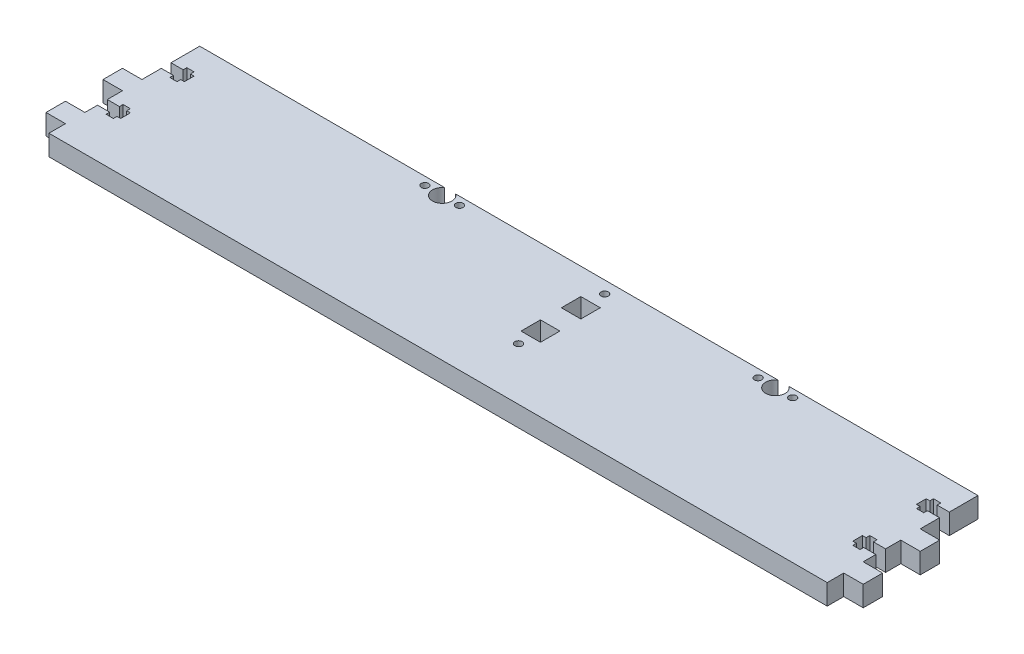
SolidWorks part; units mm, degrees
ref_plane "Front Plane" through (0, 0, 0) normal (0, 0, 1) x (1, 0, 0)
ref_plane "Top Plane" through (0, 0, 0) normal (0, 1, 0) x (1, 0, 0)
ref_plane "Right Plane" through (0, 0, 0) normal (1, 0, 0) x (0, 0, -1)
sketch "Sketch1" plane through (0, 0, 0) normal (0, 1, 0) x (1, 0, 0)
  line L0 (0, 31) -> (0, -31) construction
  line L1 (-160, 31) -> (-59.2605, 31)
  line L2 (-160, 31) -> (-160, 19.2)
  line L3 (-160, -31) -> (160, -31)
  line L4 (160, 31) -> (160, 19.2)
  line L5 (-160, 31) -> (160, -31) construction
  line L6 (-160, -31) -> (160, 31) construction
  line L7 (11.5, 31) -> (11.5, -31) construction
  line L8 (80, 27.7) -> (80, 23.7) construction
  line L9 (72.9, 27.7) -> (87.1, 27.7) construction
  line L10 (82.2605, 31) -> (160, 31)
  line L11 (160, 17.2) -> (150.5, 17.2) construction
  line L12 (160, 19.2) -> (155, 19.2)
  line L13 (155, 19.2) -> (155, 20.7)
  line L14 (155, 20.7) -> (152, 20.7)
  line L15 (152, 20.7) -> (152, 19.2)
  line L16 (152, 19.2) -> (150.5, 19.2)
  line L17 (150.5, 19.2) -> (150.5, 15.2)
  line L18 (152, 15.2) -> (150.5, 15.2)
  line L19 (152, 13.7) -> (152, 15.2)
  line L20 (155, 13.7) -> (152, 13.7)
  line L21 (155, 15.2) -> (155, 13.7)
  line L22 (160, 15.2) -> (155, 15.2)
  line L23 (160, 15.2) -> (160, 7.2486)
  line L24 (160, 4.1) -> (0, 4.1) construction
  line L25 (160, -9) -> (150.5, -9) construction
  line L26 (160, -7) -> (155, -7)
  line L27 (155, -7) -> (155, -5.5)
  line L28 (155, -5.5) -> (152, -5.5)
  line L29 (152, -5.5) -> (152, -7)
  line L30 (152, -7) -> (150.5, -7)
  line L31 (150.5, -11) -> (150.5, -7)
  line L32 (152, -11) -> (150.5, -11)
  line L33 (152, -12.5) -> (152, -11)
  line L34 (155, -12.5) -> (152, -12.5)
  line L35 (155, -11) -> (155, -12.5)
  line L36 (160, -11) -> (155, -11)
  line L37 (160, -11) -> (160, -16.2)
  line L38 (160, 7.2486) -> (168, 7.2486)
  line L39 (168, 7.2486) -> (168, -0.7514)
  line L40 (168, -0.7514) -> (160, -0.7514)
  line L41 (160, -8.4757) -> (0, -8.4757) construction
  line L42 (168, -16.2) -> (160, -16.2)
  line L43 (168, -24.2) -> (168, -16.2)
  line L44 (160, -24.2) -> (168, -24.2)
  line L45 (160, -24.2) -> (160, -31)
  line L46 (160, -0.7514) -> (160, -7)
  line L47 (-49.9, 27.7) -> (-64.1, 27.7) construction
  line L48 (-57, 27.7) -> (-57, 23.7) construction
  line L49 (-160, -9) -> (-150.5, -9) construction
  line L50 (-160, 17.2) -> (-150.5, 17.2) construction
  line L51 (-160, -0.7514) -> (-160, -7)
  line L52 (-160, -24.2) -> (-168, -24.2)
  line L53 (-168, -24.2) -> (-168, -16.2)
  line L54 (-168, -16.2) -> (-160, -16.2)
  line L55 (-168, -0.7514) -> (-160, -0.7514)
  line L56 (-168, 7.2486) -> (-168, -0.7514)
  line L57 (-160, 7.2486) -> (-168, 7.2486)
  line L58 (-160, -11) -> (-160, -16.2)
  line L59 (-160, -11) -> (-155, -11)
  line L60 (-155, -11) -> (-155, -12.5)
  line L61 (-155, -12.5) -> (-152, -12.5)
  line L62 (-152, -12.5) -> (-152, -11)
  line L63 (-152, -11) -> (-150.5, -11)
  line L64 (-150.5, -11) -> (-150.5, -7)
  line L65 (-152, -7) -> (-150.5, -7)
  line L66 (-152, -5.5) -> (-152, -7)
  line L67 (-155, -5.5) -> (-152, -5.5)
  line L68 (-155, -7) -> (-155, -5.5)
  line L69 (-160, -7) -> (-155, -7)
  line L70 (-160, 15.2) -> (-160, 7.2486)
  line L71 (-160, 15.2) -> (-155, 15.2)
  line L72 (-155, 15.2) -> (-155, 13.7)
  line L73 (-155, 13.7) -> (-152, 13.7)
  line L74 (-152, 13.7) -> (-152, 15.2)
  line L75 (-152, 15.2) -> (-150.5, 15.2)
  line L76 (-150.5, 19.2) -> (-150.5, 15.2)
  line L77 (-152, 19.2) -> (-150.5, 19.2)
  line L78 (-152, 20.7) -> (-152, 19.2)
  line L79 (-155, 20.7) -> (-152, 20.7)
  line L80 (-155, 19.2) -> (-155, 20.7)
  line L81 (-160, 19.2) -> (-155, 19.2)
  line L82 (-160, -0.7514) -> (-160, -7)
  line L83 (-160, -24.2) -> (-160, -31)
  line L84 (-160, -11) -> (-160, -16.2)
  line L85 (-160, 15.2) -> (-160, 7.2486)
  line L86 (-54.7395, 31) -> (77.7395, 31)
  line L87 (15.5, 20.2) -> (15.5, -4.4) construction
  line L88 (7.5, 3.6) -> (15.5, 3.6)
  line L89 (7.5, 3.6) -> (7.5, -4.4)
  line L90 (7.5, -4.4) -> (15.5, -4.4)
  line L91 (15.5, 3.6) -> (15.5, -4.4)
  line L92 (7.5, 3.6) -> (15.5, -4.4) construction
  line L93 (7.5, -4.4) -> (15.5, 3.6) construction
  line L94 (7.5, 20.2) -> (15.5, 20.2)
  line L95 (7.5, 20.2) -> (7.5, 12.2)
  line L96 (7.5, 12.2) -> (15.5, 12.2)
  line L97 (15.5, 20.2) -> (15.5, 12.2)
  line L98 (7.5, 20.2) -> (15.5, 12.2) construction
  line L99 (7.5, 12.2) -> (15.5, 20.2) construction
  line L100 (168, 3.2486) -> (160, 3.2486) construction
  line L101 (168, -20.2) -> (160, -20.2) construction
  arc A0 (77.7395, 31) -> (82.2605, 31) centre (80, 27.7) ccw
  circle A1 centre (87.1, 27.7) radius 1.5
  circle A2 centre (72.9, 27.7) radius 1.5
  circle A3 centre (-49.9, 27.7) radius 1.5
  circle A4 centre (-64.1, 27.7) radius 1.5
  arc A5 (-54.7395, 31) -> (-59.2605, 31) centre (-57, 27.7) cw
  circle A6 centre (11.5, 26) radius 1.5
  circle A7 centre (11.5, -9.4) radius 1.5
  point P0 (0, 0)
  point P106 (11.5, -0.4)
  point P111 (11.5, 16.2)
  dimension "D7" = 4
  dimension "D8" = 3
  dimension "D9" = 0
  dimension "D25" = 3
  dimension "D26" = 3
  dimension "D1" = 320
  dimension "D2" = 62
  dimension "D3" = 11.5
  dimension "D4" = 14.2
  dimension "D5" = 2
  dimension "D6" = 68.5
  dimension "D10" = 3.3
  dimension "D11" = 3
  dimension "D12" = 1.5
  dimension "D13" = 1.5
  dimension "D14" = 5
  dimension "D15" = 11.8
  dimension "D16" = 20
  dimension "D17" = 8
  dimension "D18" = 8
  dimension "D19" = 7.9514
  dimension "D20" = 6.8
  dimension "D21" = 8
  dimension "D22" = 8
  dimension "D23" = 8
  dimension "D24" = 16.6
  dimension "D27" = 35.4
  dimension "D28" = 9.8
  dimension "D29" = 5
extrude "Boss-Extrude1" add sketch "Sketch1" along normal blind 8.4 contours L1 A5 L2 L81 L80 L79 L78 L77 L76 L75 L74 L73 L72 L71 L70 L57 L56 L55 L51 L69 L68 L67 L66 L65 L64 L63 L62 L61 L60 L59 L58 L54 L53 L52 L83 L3 L45 L44 L43 L42 L37 L36 L35 L34 L33 L32 L31 L30 L29 L28
